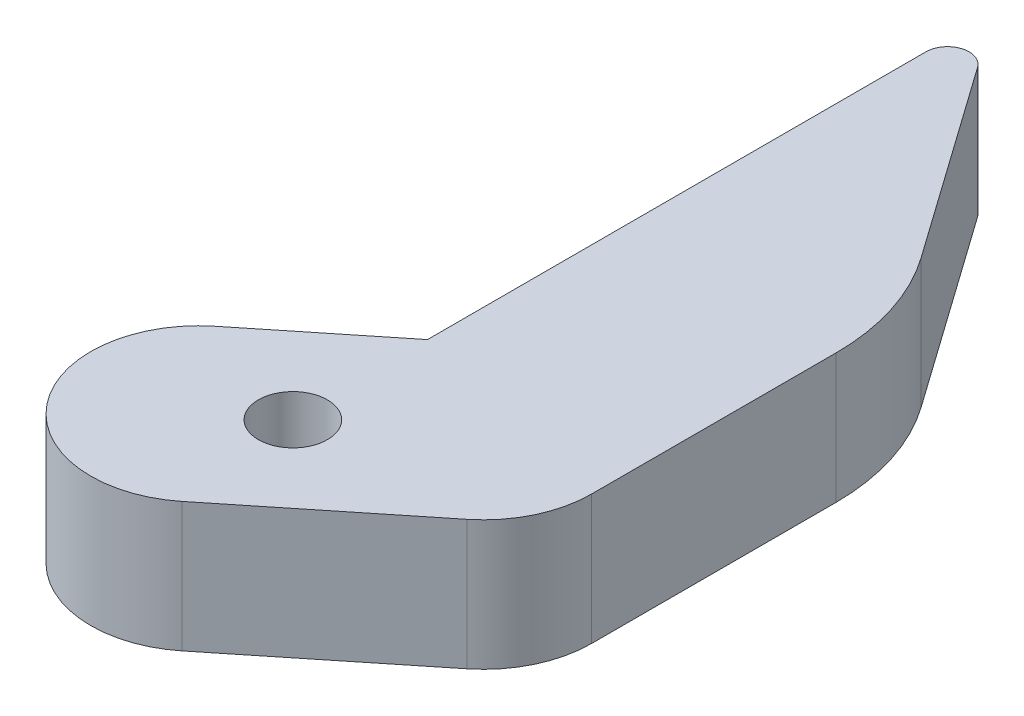
SolidWorks part; units mm, degrees
material "MDF"
ref_plane "Plano frontal" through (0, 0, 0) normal (0, 0, 1) x (1, 0, 0)
ref_plane "Plano superior" through (0, 0, 0) normal (0, 1, 0) x (1, 0, 0)
ref_plane "Plano direito" through (0, 0, 0) normal (1, 0, 0) x (0, 0, -1)
ref_plane "Plano1" through (0, -12, 0) normal (0, -1, 0) x (1, 0, 0)
sketch "Esboço1" plane through (0, -12, 0) normal (0, -1, 0) x (1, 0, 0)
  line L0 (-5.5544, -1.9504) -> (-0.0984, -6.3359)
  line L1 (-0.0984, -6.3359) -> (-0.0984, -23.4342)
  line L2 (9.9016, -12.4543) -> (9.9016, -3.9398)
  line L3 (8.034, -0.0427) -> (0.7105, 5.8439)
  line L4 (0, 0) -> (-28.7366, 23.0979) construction
  line L5 (-3.1324, -3.8971) -> (3.1324, 3.8971) construction
  arc A0 (0.7105, 5.8439) -> (-5.5544, -1.9504) centre (-2.422, 1.9467) ccw
  arc A1 (-0.0984, -23.4342) -> (2.5451, -24.405) centre (1.4016, -23.4342) ccw
  arc A2 (2.5451, -24.405) -> (9.2207, -14.9732) centre (-47.5984, 18.1641) ccw
  arc A3 (9.2207, -14.9732) -> (9.9016, -12.4543) centre (4.9016, -12.4543) ccw
  arc A4 (9.9016, -3.9398) -> (8.034, -0.0427) centre (4.9016, -3.9398) ccw
  circle A5 centre (0, 0) radius 1.6
  dimension "D1" = 3.2
  dimension "D3" = 1.5
  dimension "D7" = 23.4342
  dimension "D8" = 65.7761
  dimension "D2" = 10
  dimension "D4" = 10
  dimension "D5" = 6.2887
  dimension "D6" = 3.1073
  dimension "D9" = 6.3359
  dimension "D10" = 12.4543
extrude "Ressalto-extrusão1" add sketch "Esboço1" against normal blind 6
sketch "Esboço2" plane through (0, -12, 0) normal (0, -1, 0) x (1, 0, 0)
  line L0 (-0.0984, -23.4342) -> (-0.0984, -32.578)
  line L1 (-0.0984, -32.578) -> (9.9016, -18.4494)
  line L2 (9.9016, -18.4494) -> (9.9016, -12.4543)
  line L3 (2.5451, -24.405) -> (2.5451, -28.8431) construction
  line L4 (9.2207, -14.9732) -> (9.2207, -19.4114) construction
  arc A0 (2.5451, -24.405) -> (9.2207, -14.9732) centre (-47.5984, 18.1641) ccw construction
  arc A1 (2.5451, -24.405) -> (9.2207, -14.9732) centre (-47.5984, 18.1641) ccw
  arc A2 (-0.0984, -29.4342) -> (1.7178, -30.0119) centre (0.9016, -29.4342) ccw
  arc M10 (-0.0984, -23.4342) -> (2.5451, -24.405) centre (1.4016, -23.4342) ccw
  arc M11 (2.5451, -24.405) -> (9.2207, -14.9732) centre (-47.5984, 18.1641) ccw
  arc M12 (9.2207, -14.9732) -> (9.9016, -12.4543) centre (4.9016, -12.4543) ccw
  dimension "D1" = 1
  dimension "D2" = 6
extrude "Ressalto-extrusão2" add sketch "Esboço2" against normal up to surface (6 mm away) contours L0 A2 L1 L2 M12 M11 M10 up to face at (0, -6, 1.6)
fillet "Filete1" radius 10 1 edges at (9.9016, -9, -18.4494)
